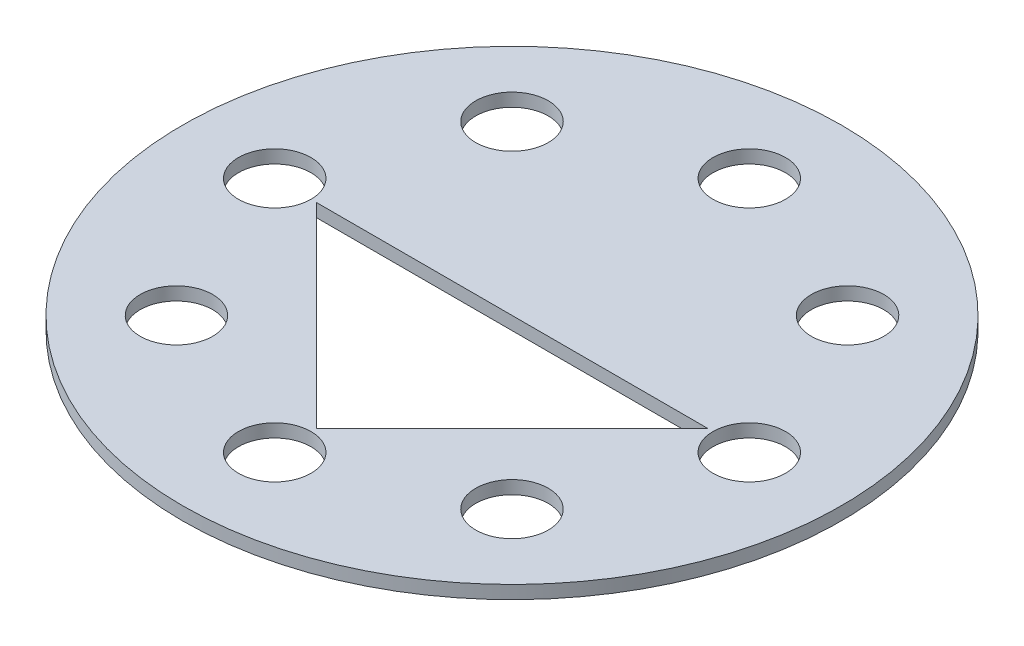
SolidWorks part; units mm, degrees
ref_plane "前视基准面" through (0, 0, 0) normal (0, 0, 1) x (1, 0, 0)
ref_plane "上视基准面" through (0, 0, 0) normal (0, 1, 0) x (1, 0, 0)
ref_plane "右视基准面" through (0, 0, 0) normal (1, 0, 0) x (0, 0, -1)
sketch "草图1" plane through (0, 0, 0) normal (0, 1, 0) x (1, 0, 0)
  circle A0 centre (0, 0) radius 25
  dimension "D1" = 50
extrude "凸台-拉伸2" add sketch "草图1" along normal blind 1
sketch "草图2" plane through (0, 1, 0) normal (0, 1, 0) x (1, 0, 0)
  circle A0 centre (18, 0) radius 1.5
  dimension "D2" = 3
extrude "切除-拉伸1" cut sketch "草图2" against normal blind 1
pattern_circular "阵列(圆周)1" count 8 over 360 about axis through (0, 0, 0) along (0, 1, 0) of "切除-拉伸1"
sketch "草图3" plane through (0, 1, 0) normal (0, 1, 0) x (1, 0, 0)
  line L0 (-15.2028, 0) -> (15.2028, 0)
  line L2 (15.2028, 0) -> (0, -15.2028)
  line L3 (0, -15.2028) -> (-15.2028, 0)
  dimension "D1" = 21.5
  dimension "D3" = 21.5
extrude "切除-拉伸2" cut sketch "草图3" against normal blind 1
sketch "草图4" plane through (0, 1, 0) normal (0, 1, 0) x (1, 0, 0)
  line L0 (0, -14.8492) -> (14.8492, 0)
  line L2 (15.2028, 0) -> (-15.2028, 0) construction
  line L4 (0, -14.8492) -> (-14.8492, 0)
  line L6 (-14.8492, 0) -> (-15.2028, 0)
  line L7 (-15.2028, 0) -> (0, -15.2028)
  line L8 (0, -15.2028) -> (15.2028, 0)
  line L9 (15.2028, 0) -> (14.8492, 0)
extrude "凸台-拉伸3" add sketch "草图4" against normal blind 1
sketch "草图5" plane through (0, 0, 0) normal (0, -1, 0) x (1, 0, 0)
  circle A0 centre (0, 0) radius 25
extrude "凸台-拉伸5" add sketch "草图5" along normal blind 2
sketch "草图6" plane through (0, 0, 0) normal (0, 1, 0) x (1, 0, 0)
  circle A0 centre (18, 0) radius 1.5
  dimension "D1" = 3
extrude "切除-拉伸3" cut sketch "草图6" against normal blind 2
pattern_circular "阵列(圆周)2" count 8 over 360 about axis through (0, 0, 0) along (0, 1, 0) of "切除-拉伸3"
sketch "草图7" plane through (0, 1, 0) normal (0, 1, 0) x (1, 0, 0)
  line L0 (-14.8492, 0) -> (14.8492, 0)
  line L1 (14.8492, 0) -> (0, -14.8492)
  line L2 (0, -14.8492) -> (-14.8492, 0)
  circle A0 centre (0, 0) radius 25
sketch "草图8" plane through (0, 1, 0) normal (0, 1, 0) x (1, 0, 0)
  circle A0 centre (18, 0) radius 2.75
  dimension "D1" = 5.5
extrude "凸台-拉伸6" add sketch "草图7" along normal blind 2
extrude "切除-拉伸4" cut sketch "草图8" along normal blind 2
pattern_circular "阵列(圆周)3" count 8 over 360 about axis through (0, 0, 0) along (0, 1, 0) of "切除-拉伸4"
sketch "草图9" plane through (0, 0, 0) normal (0, 1, 0) x (1, 0, 0)
  line L0 (-14.8492, 0) -> (14.8492, 0)
  line L1 (14.8492, 0) -> (0, -14.8492)
  line L2 (0, -14.8492) -> (-14.8492, 0)
extrude "凸台-拉伸8" add sketch "草图9" along normal blind 2
sketch "草图11" plane through (0, -2, 0) normal (0, -1, 0) x (1, 0, 0)
  circle A0 centre (0, 0) radius 25
extrude "切除-拉伸6" cut sketch "草图11" against normal blind 4
